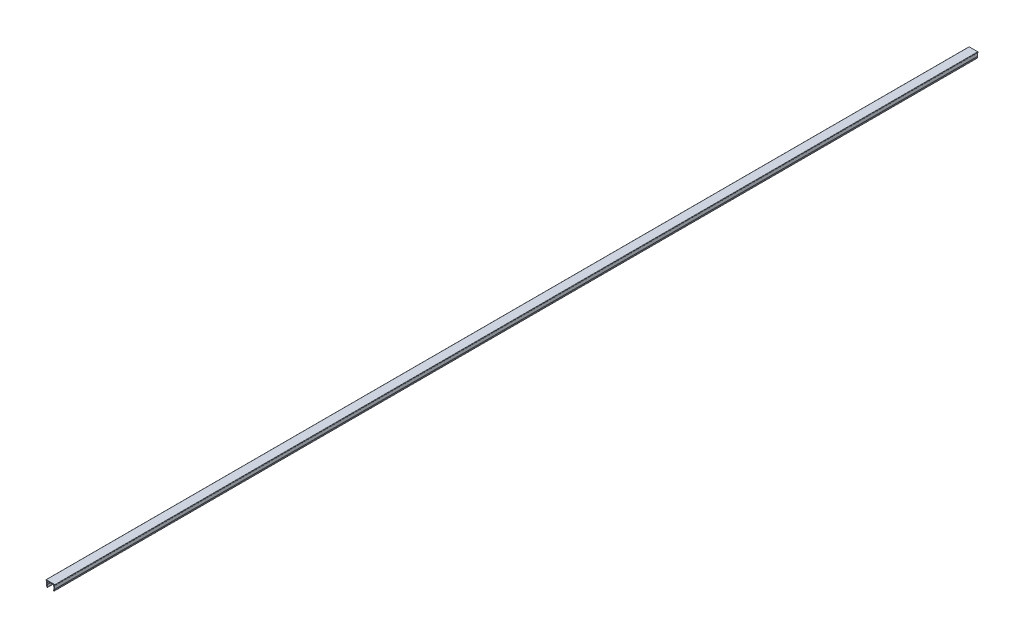
SolidWorks part; units mm, degrees
ref_plane "前视基准面" through (0, 0, 0) normal (0, 0, 1) x (1, 0, 0)
ref_plane "上视基准面" through (0, 0, 0) normal (0, 1, 0) x (1, 0, 0)
ref_plane "右视基准面" through (0, 0, 0) normal (1, 0, 0) x (0, 0, -1)
sketch "草图1" plane through (0, 0, 0) normal (0, 0, 1) x (1, 0, 0)
  line L1 (9.9576, 89.4833) -> (10.6003, 91.249)
  line L2 (11.3666, 91.0155) -> (10.7094, 89.2097)
  line L3 (10.8267, 94.8494) -> (11.4118, 91.5312)
  line L4 (11.5115, 94.8494) -> (10.8267, 94.8494)
  line L5 (11.7115, 95.3494) -> (11.7115, 95.0494)
  line L6 (2.2115, 95.6494) -> (11.4115, 95.6494)
  line L7 (1.9115, 95.0494) -> (1.9115, 95.3494)
  line L8 (2.7947, 94.8494) -> (2.1115, 94.8494)
  line L9 (2.2112, 91.5401) -> (2.7947, 94.8494)
  line L10 (2.9136, 89.2186) -> (2.2563, 91.0244)
  line L11 (3.0238, 91.2549) -> (3.6653, 89.4922)
  line L12 (3.61, 94.8494) -> (3.008, 91.4354)
  line L13 (10.013, 94.8494) -> (3.61, 94.8494)
  line L14 (10.6161, 91.4295) -> (10.013, 94.8494)
  arc A0 (10.6003, 91.249) -> (10.6161, 91.4295) centre (10.2714, 91.3687) ccw
  arc A1 (9.9576, 89.4833) -> (10.7094, 89.2097) centre (10.3335, 89.3465) ccw
  arc A2 (11.3666, 91.0155) -> (11.4118, 91.5312) centre (10.4269, 91.3575) ccw
  arc A3 (11.5115, 94.8494) -> (11.7115, 95.0494) centre (11.5115, 95.0494) ccw
  arc A4 (11.7115, 95.3494) -> (11.4115, 95.6494) centre (11.4115, 95.3494) ccw
  arc A5 (2.2115, 95.6494) -> (1.9115, 95.3494) centre (2.2115, 95.3494) ccw
  arc A6 (1.9115, 95.0494) -> (2.1115, 94.8494) centre (2.1115, 95.0494) ccw
  arc A7 (2.2112, 91.5401) -> (2.2563, 91.0244) centre (3.196, 91.3664) ccw
  arc A8 (2.9136, 89.2186) -> (3.6653, 89.4922) centre (3.2895, 89.3554) ccw
  arc A9 (3.008, 91.4354) -> (3.0238, 91.2549) centre (3.3527, 91.3746) ccw
extrude "拉伸1" add sketch "草图1" along normal blind 1000
